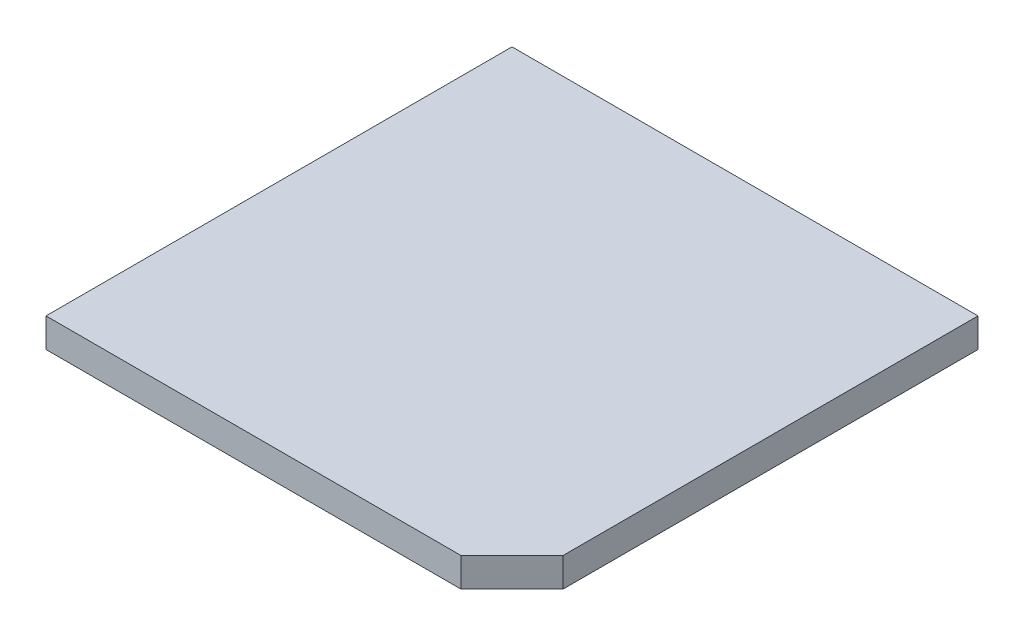
SolidWorks part; units mm, degrees
material "1060-H16"
ref_plane "Front Plane" through (0, 0, 0) normal (0, 0, 1) x (1, 0, 0)
ref_plane "Top Plane" through (0, 0, 0) normal (0, 1, 0) x (1, 0, 0)
ref_plane "Right Plane" through (0, 0, 0) normal (1, 0, 0) x (0, 0, -1)
sketch "Sketch1" plane through (0, 0, 0) normal (0, 1, 0) x (1, 0, 0)
  line L1 (-1.6, 1.6) -> (1.6, 1.6)
  line L2 (-1.6, 1.6) -> (-1.6, -1.6)
  line L3 (-1.6, -1.6) -> (1.6, -1.6)
  line L4 (1.6, 1.6) -> (1.6, -1.6)
  line L5 (-1.6, 1.6) -> (1.6, -1.6) construction
  line L6 (-1.6, -1.6) -> (1.6, 1.6) construction
  point P0 (0, 0)
  dimension "D1" = 3.2
extrude "Boss-Extrude1" add sketch "Sketch1" along normal blind 0.2
chamfer "Chamfer1" distance 0.35 angle 45 1 edges at (1.6, 0.1, 1.6)
